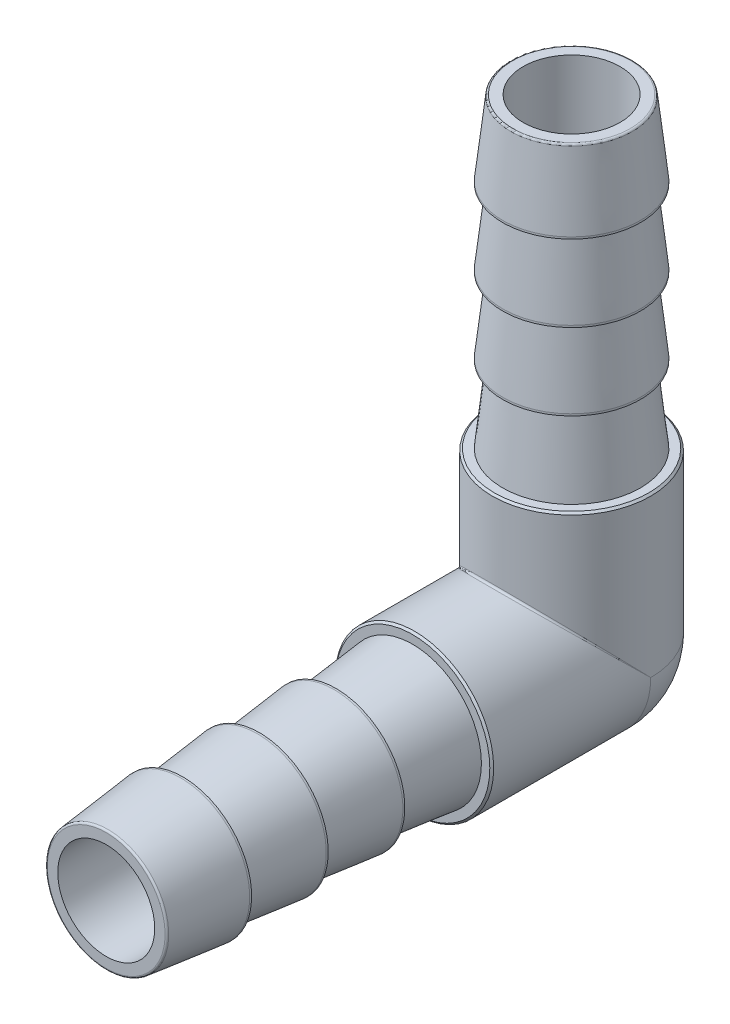
SolidWorks part; units mm, degrees
ref_plane "Front Plane" through (0, 0, 0) normal (0, 0, 1) x (1, 0, 0)
ref_plane "Top Plane" through (0, 0, 0) normal (0, 1, 0) x (1, 0, 0)
ref_plane "Right Plane" through (0, 0, 0) normal (1, 0, 0) x (0, 0, -1)
sketch "Sketch1" plane through (0, 0, 0) normal (1, 0, 0) x (0, 0, -1)
  line L0 (-30.48, 0) -> (0, 0) construction
  line L2 (-3.175, 30.48) -> (3.175, 30.48) construction
  line L3 (-30.48, 3.9688) -> (-30.48, -3.9688) construction
  line L5 (0, 5.1848) -> (0, -5.1848) construction
  line L6 (-30.48, 3.175) -> (-30.48, -3.175) construction
  line L7 (-30.48, 4.5085) -> (-30.48, -4.5085) construction
  line L8 (-3.9688, 30.48) -> (3.9688, 30.48) construction
  line L11 (-10.414, 5.1848) -> (-10.414, -5.1848) construction
  line L12 (-5.1848, 10.414) -> (5.1848, 10.414) construction
  line L13 (5.1848, 10.414) -> (5.1848, -5.1848) construction
  line L14 (0, 0) -> (0, 30.48) construction
  line L15 (-10.414, -5.1848) -> (5.1848, -5.1848) construction
  point P1 (-10.414, 0)
  point P32 (0, 10.414)
  dimension "ID" = 6.35
  dimension "Barb End Length" = 20.066
  dimension "Barb End Length2" = 20.066
  dimension "D2" = 10.3696
  dimension "Length" = 30.48
  dimension "For Hose ID" = 7.9375
  dimension "Barb OD" = 9.017
sketch "Sketch2" plane through (0, 0, 0) normal (1, 0, 0) x (0, 0, -1)
  line L1 (-30.48, 0) -> (-30.48, 5.1848)
  line L2 (0, 0) -> (0, 5.1848) construction
  line L3 (-30.48, 5.1848) -> (0, 5.1848)
  line L4 (0, 5.1848) -> (0, -5.1848) construction
  line L9 (-30.48, 0) -> (0, 0) construction
  line L12 (5.1848, 0) -> (-30.48, 0)
  arc A0 (5.1848, 0) -> (0, 5.1848) centre (0, 0) ccw
revolve "Revolve1" add sketch "Sketch2" angle 360 about L9
sketch "Sketch3" plane through (0, 0, 0) normal (1, 0, 0) x (0, 0, -1)
  line L0 (-30.48, 5.1848) -> (-30.48, 3.9688)
  line L1 (-30.48, 5.1848) -> (-10.414, 5.1848)
  line L2 (-30.48, 3.9688) -> (-15.4305, 3.9688)
  line L3 (-30.48, 0) -> (0, 0) construction
  line L5 (-10.414, 5.1848) -> (-10.414, -5.1848) construction
  line L6 (-10.414, 4.5085) -> (-15.4305, 3.9688)
  line L12 (-10.414, 4.5085) -> (-10.414, 5.1848)
  dimension "D1" = 5.0165
revolve "Cut-Revolve1" cut sketch "Sketch3" angle 360 about L3
sketch "Sketch4" plane through (0, 0, 0) normal (1, 0, 0) x (0, 0, -1)
  line L0 (-10.414, 0) -> (-30.48, 0) construction
  line L1 (-30.48, 3.9688) -> (-30.48, -3.9688) construction
  line L2 (-25.4635, 4.5085) -> (-25.5905, 4.5085)
  line L4 (-25.4635, 3.9687) -> (-25.4635, 4.5085)
  line L5 (-25.5905, 4.5085) -> (-30.48, 3.9688)
  line L7 (-25.4635, 3.9687) -> (-30.48, 3.9688)
  dimension "D2" = 5.0165
  dimension "D1" = 0.127
revolve "Revolve2" add sketch "Sketch4" angle 360 about L0
pattern_linear "LPattern1" count 3 spacing 5.0165 along (0, 0, -1) of "Revolve2"
chamfer "Chamfer1" distance 0.127 angle 45 1 edges at (5.1848, 0, 10.414)
ref_axis "Axis1" through (-6.6672, 0, 0) along (1, 0, 0)
pattern_circular "CirPattern1" count 2 over 90 about axis through (-6.6672, 0, 0) along (1, 0, 0) of "Revolve1", "Cut-Revolve1", "Revolve2", "LPattern1", "Chamfer1"
sketch "Sketch5" plane through (0, 0, 0) normal (1, 0, 0) x (0, 0, -1)
  line L0 (0, 5.1848) -> (0, -5.1848) construction
  line L1 (-30.48, 3.175) -> (0, 3.175)
  line L2 (-30.48, 3.175) -> (-30.48, 0)
  line L3 (-30.48, 0) -> (3.175, 0)
  arc A0 (3.175, 0) -> (0, 3.175) centre (0, 0) ccw
revolve "Cut-Revolve2" cut sketch "Sketch5" angle 360 about L3
pattern_circular "CirPattern2" count 2 every 90 about axis through (-6.6672, 0, 0) along (1, 0, 0) of "Cut-Revolve2"
fillet "Fillet2" radius 0.127 3 edges at (0, 5.1848, 5.1848) (-3.9688, 30.48, 0) (-3.9688, 0, 30.48)
equation "\"Barb End Length2@Sketch1\" = \"Barb End Length@Sketch1\""
equation "\"D2@Sketch4\" = \"Barb End Length@Sketch1\" /  ( \"No. of Barbs@LPattern1\" + 1 ) "
equation "\"D1@Sketch3\"=\"D2@Sketch4\""
equation "\"D3@LPattern1\" = \"D2@Sketch4\""
equation "\"D2@Sketch1\"=\"Barb OD@Sketch1\"*1.15"
